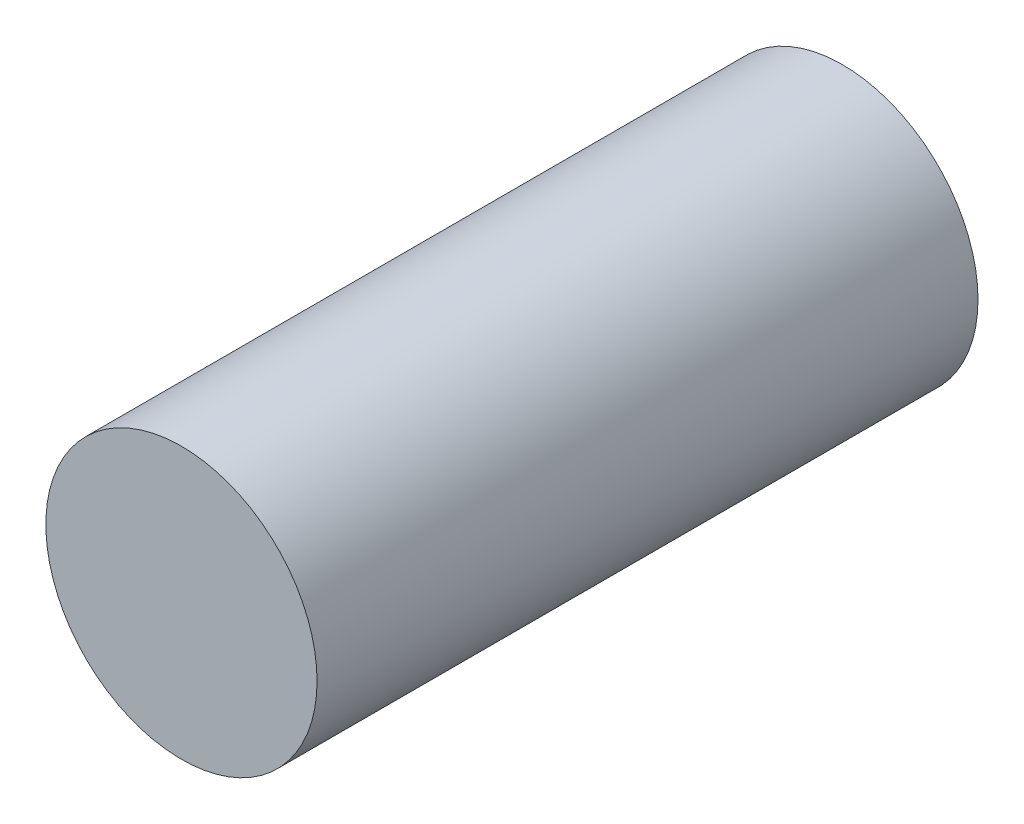
SolidWorks part; units mm, degrees
ref_plane "Front Plane" through (0, 0, 0) normal (0, 0, 1) x (1, 0, 0)
ref_plane "Top Plane" through (0, 0, 0) normal (0, 1, 0) x (1, 0, 0)
ref_plane "Right Plane" through (0, 0, 0) normal (1, 0, 0) x (0, 0, -1)
sketch "Sketch1" plane through (0, 0, 0) normal (0, 0, 1) x (1, 0, 0)
  circle A0 centre (-18.4959, 12.9398) radius 5.95
  dimension "D1" = 11.9
extrude "Boss-Extrude1" add sketch "Sketch1" along normal blind 29
